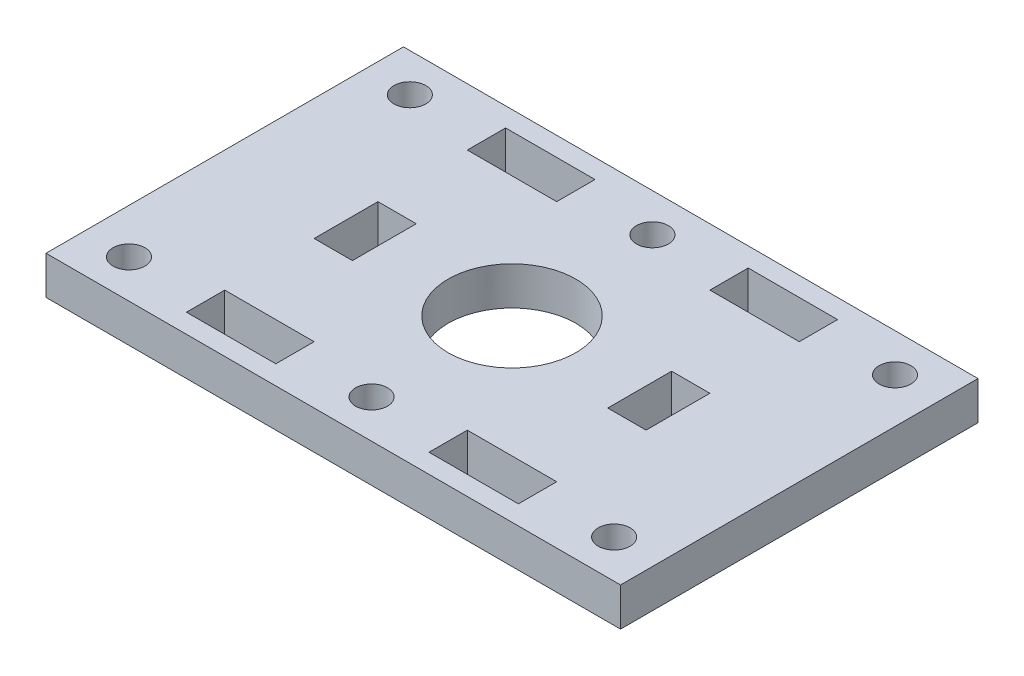
SolidWorks part; units mm, degrees
ref_plane "정면" through (0, 0, 0) normal (0, 0, 1) x (1, 0, 0)
ref_plane "윗면" through (0, 0, 0) normal (0, 1, 0) x (1, 0, 0)
ref_plane "우측면" through (0, 0, 0) normal (1, 0, 0) x (0, 0, -1)
sketch "스케치1" plane through (0, 0, 0) normal (0, 1, 0) x (1, 0, 0)
  line L1 (0, 0) -> (45, 0)
  line L2 (0, 0) -> (0, 28)
  line L3 (0, 28) -> (45, 28)
  line L4 (45, 0) -> (45, 28)
  dimension "D1" = 28
  dimension "D2" = 45
extrude "보스-돌출1" add sketch "스케치1" along normal blind 3
sketch "스케치2" plane through (0, 3, 0) normal (0, 1, 0) x (1, 0, 0)
  line L0 (0, 28) -> (0, 0) construction
  line L1 (-9.4122, 14) -> (48.0652, 14) construction
  line L2 (22.5, 30.6218) -> (22.5, -1.6898) construction
  line L3 (0, 0) -> (45, 0) construction
  line L8 (35.5, 1.5) -> (28.5, 1.5)
  line L9 (28.5, 4.5) -> (28.5, 1.5)
  line L10 (9.5, 4.5) -> (16.5, 4.5)
  line L11 (9.5, 4.5) -> (9.5, 1.5)
  line L12 (9.5, 1.5) -> (16.5, 1.5)
  line L13 (16.5, 4.5) -> (16.5, 1.5)
  line L14 (35.5, 4.5) -> (28.5, 4.5)
  line L15 (35.5, 4.5) -> (35.5, 1.5)
  line L16 (35.5, 23.5) -> (35.5, 26.5)
  line L17 (35.5, 23.5) -> (28.5, 23.5)
  line L18 (28.5, 23.5) -> (28.5, 26.5)
  line L19 (35.5, 26.5) -> (28.5, 26.5)
  line L20 (9.5, 26.5) -> (16.5, 26.5)
  line L21 (16.5, 23.5) -> (16.5, 26.5)
  line L22 (9.5, 23.5) -> (16.5, 23.5)
  line L23 (9.5, 23.5) -> (9.5, 26.5)
  circle A0 centre (22.5, 3) radius 1.25
  circle A1 centre (22.5, 25) radius 1.25
  circle A2 centre (3.5, 3) radius 1.25
  circle A3 centre (41.5, 3) radius 1.25
  circle A4 centre (41.5, 25) radius 1.25
  circle A5 centre (3.5, 25) radius 1.25
  point P0 (0, 3)
  point P1 (0, 14)
  point P12 (3.5, 0)
  dimension "D2" = 2.5
  dimension "D4" = 2.5
  dimension "D5" = 22.5
  dimension "D1" = 11
  dimension "D3" = 19
  dimension "D6" = 19
  dimension "D7" = 1.5
  dimension "D8" = 3
  dimension "D9" = 7
  dimension "D10" = 6
extrude "컷-돌출1" cut sketch "스케치2" against normal through all
sketch "스케치3" plane through (0, 3, 0) normal (0, 1, 0) x (1, 0, 0)
  line L1 (9.5, 11.5) -> (12.5, 11.5)
  line L2 (9.5, 11.5) -> (9.5, 16.5)
  line L3 (9.5, 16.5) -> (12.5, 16.5)
  line L4 (12.5, 11.5) -> (12.5, 16.5)
  line L5 (9.5, 26.5) -> (9.5, 23.5) construction
  line L6 (22.5, -5.8736) -> (22.5, 33.7013) construction
  line L7 (35.5, 16.5) -> (32.5, 16.5)
  line L8 (32.5, 11.5) -> (32.5, 16.5)
  line L9 (35.5, 11.5) -> (32.5, 11.5)
  line L10 (35.5, 11.5) -> (35.5, 16.5)
  dimension "D1" = 5
  dimension "D2" = 11.5
  dimension "D3" = 3
extrude "컷-돌출2" cut sketch "스케치3" against normal through all
sketch "스케치4" plane through (0, 3, 0) normal (0, 1, 0) x (1, 0, 0)
  circle A0 centre (22.5, 14) radius 5
  dimension "D1" = 10
extrude "컷-돌출3" cut sketch "스케치4" against normal blind 10
